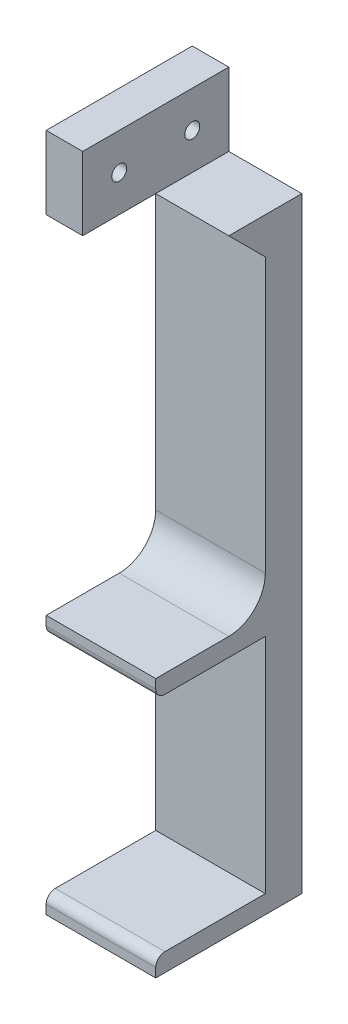
SolidWorks part; units mm, degrees
ref_plane "前基準面" through (0, 0, 0) normal (0, 0, 1) x (1, 0, 0)
ref_plane "上基準面" through (0, 0, 0) normal (0, 1, 0) x (1, 0, 0)
ref_plane "右基準面" through (0, 0, 0) normal (1, 0, 0) x (0, 0, -1)
sketch "草圖1" plane through (0, 0, 0) normal (0, 0, 1) x (1, 0, 0)
  line L1 (-11.7963, 160.3304) -> (18.2037, 160.3304)
  line L2 (-11.7963, 160.3304) -> (-11.7963, -25.6696)
  line L3 (-11.7963, -25.6696) -> (18.2037, -25.6696)
  line L4 (18.2037, 160.3304) -> (18.2037, -25.6696)
  dimension "D1" = 30
  dimension "D2" = 186
extrude "填料-伸長1" add sketch "草圖1" along normal blind 10
sketch "草圖2" plane through (0, 0, 10) normal (0, 0, 1) x (1, 0, 0)
  line L0 (18.2037, -25.6696) -> (18.2037, 160.3304) construction
  line L1 (-11.7963, -25.6696) -> (18.2037, -25.6696)
  line L2 (-11.7963, -25.6696) -> (-11.7963, -20.6696)
  line L3 (-11.7963, -20.6696) -> (18.2037, -20.6696)
  line L4 (18.2037, -25.6696) -> (18.2037, -20.6696)
  line L5 (-11.7963, 160.3304) -> (-11.7963, -25.6696) construction
  line L6 (-11.7963, 45.3304) -> (18.2037, 45.3304)
  line L7 (-11.7963, 45.3304) -> (-11.7963, 40.3304)
  line L8 (-11.7963, 40.3304) -> (18.2037, 40.3304)
  line L9 (18.2037, 45.3304) -> (18.2037, 40.3304)
  line L11 (-11.7963, 160.3304) -> (18.2037, 160.3304)
  line L12 (-11.7963, 160.3304) -> (-11.7963, 140.3304)
  line L13 (-11.7963, 140.3304) -> (18.2037, 140.3304)
  line L14 (18.2037, 160.3304) -> (18.2037, 140.3304)
  dimension "D1" = 5
  dimension "D2" = 5
  dimension "D3" = 61
  dimension "D4" = 20
extrude "填料-伸長2" add sketch "草圖2" along normal blind 30
fillet "圓角1" radius 2.5 2 edges at (3.2037, -20.6696, 40) (3.2037, 40.3304, 40)
fillet "圓角4" radius 10 1 edges at (3.2037, 45.3304, 10)
chamfer "導角7" distance 10 angle 45 1 edges at (3.2037, 140.3304, 10)
sketch "草圖9" plane through (18.2037, 0, 0) normal (1, 0, 0) x (0, 0, -1)
  line L1 (-40, 140.3304) -> (0, 140.3304)
  line L2 (-40, 140.3304) -> (-40, 160.3304)
  line L3 (-40, 160.3304) -> (0, 160.3304)
  line L4 (0, 140.3304) -> (0, 160.3304)
extrude "除料-伸長5" cut sketch "草圖9" against normal blind 20
sketch "草圖10" plane through (-11.7963, 0, 0) normal (-1, 0, 0) x (0, 0, 1)
  line L0 (40, 160.3304) -> (0, 160.3304) construction
  line L1 (0, 160.3304) -> (0, -25.6696) construction
  line L2 (40, 160.3304) -> (40, 140.3304) construction
  circle A0 centre (10, 150.3304) radius 2.05
  circle A1 centre (30, 150.3304) radius 2.05
  dimension "D1" = 4.1
  dimension "D2" = 4.1
  dimension "D3" = 10
  dimension "D4" = 10
  dimension "D5" = 10
  dimension "D6" = 10
extrude "除料-伸長6" cut sketch "草圖10" against normal blind 10
sketch "草圖11" plane through (-11.7963, 0, 0) normal (-1, 0, 0) x (0, 0, 1)
  circle A0 centre (10, 150.3304) radius 3.75
  circle A1 centre (30, 150.3304) radius 3.75
  dimension "D1" = 7.5
  dimension "D2" = 7.5
extrude "除料-伸長7" cut sketch "草圖11" against normal blind 4
